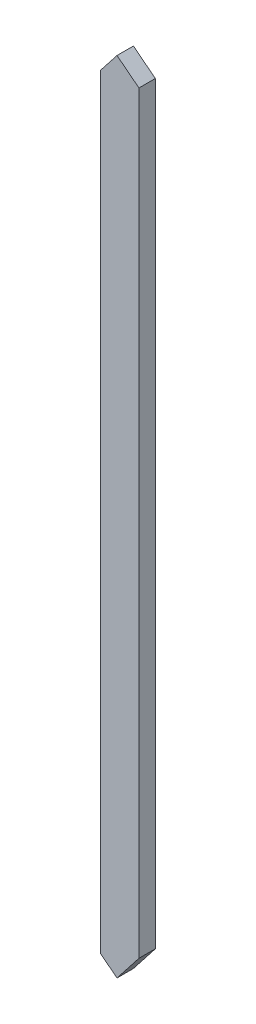
SolidWorks part; units mm, degrees
material "Oak"
ref_plane "Front Plane" through (0, 0, 0) normal (0, 0, 1) x (1, 0, 0)
ref_plane "Top Plane" through (0, 0, 0) normal (0, 1, 0) x (1, 0, 0)
ref_plane "Right Plane" through (0, 0, 0) normal (1, 0, 0) x (0, 0, -1)
sketch "Sketch1" plane through (0, 0, 0) normal (0, 1, 0) x (1, 0, 0)
  line L1 (-44.45, -19.05) -> (44.45, -19.05)
  line L2 (-44.45, -19.05) -> (-44.45, 19.05)
  line L3 (-44.45, 19.05) -> (44.45, 19.05)
  line L4 (44.45, -19.05) -> (44.45, 19.05)
  line L5 (-44.45, -19.05) -> (44.45, 19.05) construction
  line L6 (-44.45, 19.05) -> (44.45, -19.05) construction
  point P0 (0, 0)
  dimension "D1" = 38.1
  dimension "D2" = 88.9
extrude "Boss-Extrude1" add sketch "Sketch1" along normal blind 2032 contours L3 L4 L1 L2
sketch "Sketch2" plane through (0, 0, 19.05) normal (0, 0, 1) x (1, 0, 0)
  line L0 (-44.45, 2032) -> (44.45, 2032) construction
  line L5 (-6.4541, 1854.5914) -> (-44.45, 1806.0411)
  line L6 (44.45, 1814.7534) -> (-6.4541, 1854.5914)
  line L8 (44.45, 2032) -> (44.45, 0) construction
  line L9 (-44.45, 2032) -> (-44.45, 0) construction
  line L10 (44.45, 1814.7534) -> (44.45, 2032)
  line L12 (44.45, 2032) -> (-44.45, 2032)
  line L13 (-44.45, 2032) -> (-44.45, 1806.0411)
  line L14 (-44.45, 0) -> (44.45, 0) construction
  point P3 (44.45, 2065.6392)
  point P6 (42.2708, 2065.6392)
  line M8 (44.45, 0) -> (44.45, 2032)
  line M9 (44.45, 2032) -> (-44.45, 2032)
  line M10 (-44.45, 2032) -> (-44.45, 0)
  dimension "D1" = 1806.0411
  dimension "D2" = 90
  dimension "D3" = 61.6508
  dimension "D4" = 64.6397
extrude "Cut-Extrude2" cut sketch "Sketch2" against normal through all contours L6 L5 M8 M9 M10
sketch "Sketch3" plane through (0, 0, 19.05) normal (0, 0, 1) x (1, 0, 0)
  line L1 (-44.45, 1806.0411) -> (-44.45, 0) construction
  line L2 (44.45, 65.0442) -> (-6.4541, 0)
  line L3 (44.45, 1814.7534) -> (44.45, 0) construction
  line L5 (-6.4541, 0) -> (-44.45, 29.7359)
  line L6 (-44.45, 29.7359) -> (-64.2395, 4.4494)
  line L7 (-64.2395, 4.4494) -> (31.2442, -54.4301)
  line L8 (31.2442, -54.4301) -> (82.1065, 35.5738)
  line L9 (82.1065, 35.5738) -> (44.45, 65.0442)
  point P0 (44.45, 65.0442)
  point P1 (-44.45, 29.7359)
  dimension "D1" = 32.1097
  dimension "D2" = 48.2484
  dimension "D3" = 82.5952
  dimension "D4" = 47.8175
  dimension "D5" = 103.3812
  dimension "D6" = 112.1781
  dimension "D7" = 6.4541
extrude "Cut-Extrude3" cut sketch "Sketch3" against normal through all
